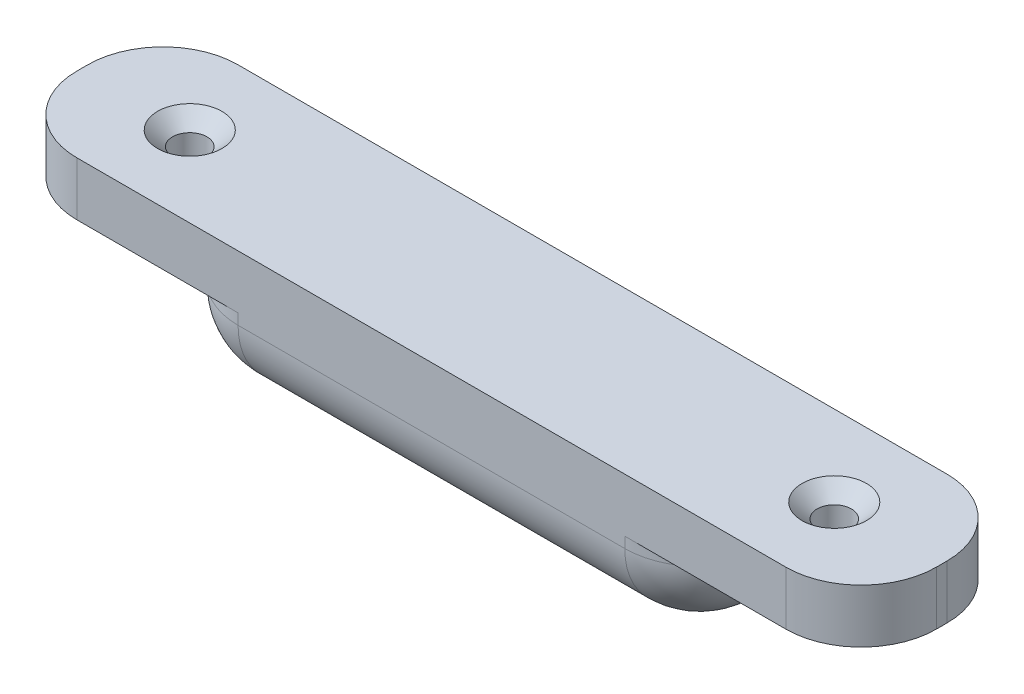
SolidWorks part; units mm, degrees
ref_plane "Plan de face" through (0, 0, 0) normal (0, 0, 1) x (1, 0, 0)
ref_plane "Plan de dessus" through (0, 0, 0) normal (0, 1, 0) x (1, 0, 0)
ref_plane "Plan de droite" through (0, 0, 0) normal (1, 0, 0) x (0, 0, -1)
sketch "Esquisse1" plane through (0, 0, 0) normal (0, 0, 1) x (1, 0, 0)
  line L0 (-40, 13) -> (-40, 8)
  line L1 (-40, 8) -> (-25, 8)
  line L2 (-25, 8) -> (-25, 0)
  line L3 (-25, 0) -> (25, 0)
  line L4 (0, 0) -> (0, 13)
  line L5 (40, 13) -> (-40, 13)
  line L6 (0, -55) -> (0, 55) construction
  line L7 (25, 8) -> (25, 0)
  line L8 (40, 8) -> (25, 8)
  line L9 (40, 13) -> (40, 8)
  dimension "D1" = 8
  dimension "D2" = 5
  dimension "D3" = 15
  dimension "D4" = 25
extrude "Boss.-Extru.1" add sketch "Esquisse1" along normal blind 15 contours L4 L5 L0 L1 L2 L3 | L9 L5 L4 L3 L7 L8
hole_wizard "Fraisage pour vis à tête fraisée cruciforme M31" positions "Esquisse2" profile "Esquisse3" countersink size "M3" standard "AS" end condition through all
sketch "Esquisse2" plane through (0, 13, 0) normal (0, 1, 0) x (1, 0, 0)
  line L0 (-30, -7.5) -> (30, -7.5) construction
  line L2 (-40, -15) -> (-40, 0) construction
  point P0 (-30, -7.5)
  point P2 (30, -7.5)
  point P9 (0, -7.5)
  point P13 (-40, -7.5)
  dimension "D1" = 10
sketch "Esquisse3" plane through (-30, 13, 7.5) normal (1, 0, 0) x (0, 0, 1)
  line L0 (0, 0) -> (0, 13)
  line L1 (0, 13) -> (1.6, 13)
  line L2 (1.6, 13) -> (1.6, 1.352)
  line L3 (1.6, 1.352) -> (3, 0)
  line L5 (3, 0) -> (0, 0)
  line L6 (-1.6, 1.352) -> (-3, 0) construction
  line L11 (0, -6.35) -> (0, 107.95) construction
  dimension "Diamètre du perçage jusqu'au prochain" = 3.2
  dimension "Profondeur du perçage jusqu'au prochain" = 13
  dimension "Diamètre du fraisage entrant" = 6
  dimension "Angle du fraisage entrant" = 92
fillet "Congé1" radius 7 12 edges at (40, 10.5, 15) (40, 10.5, 0) (0, 0, 0) (0, 0, 15) (-40, 10.5, 0) (-40, 10.5, 15) (-25, 0, 7.5) (25, 0, 7.5) (25, 4, 0) (-25, 4, 0) (-25, 4, 15) (25, 4, 15)
